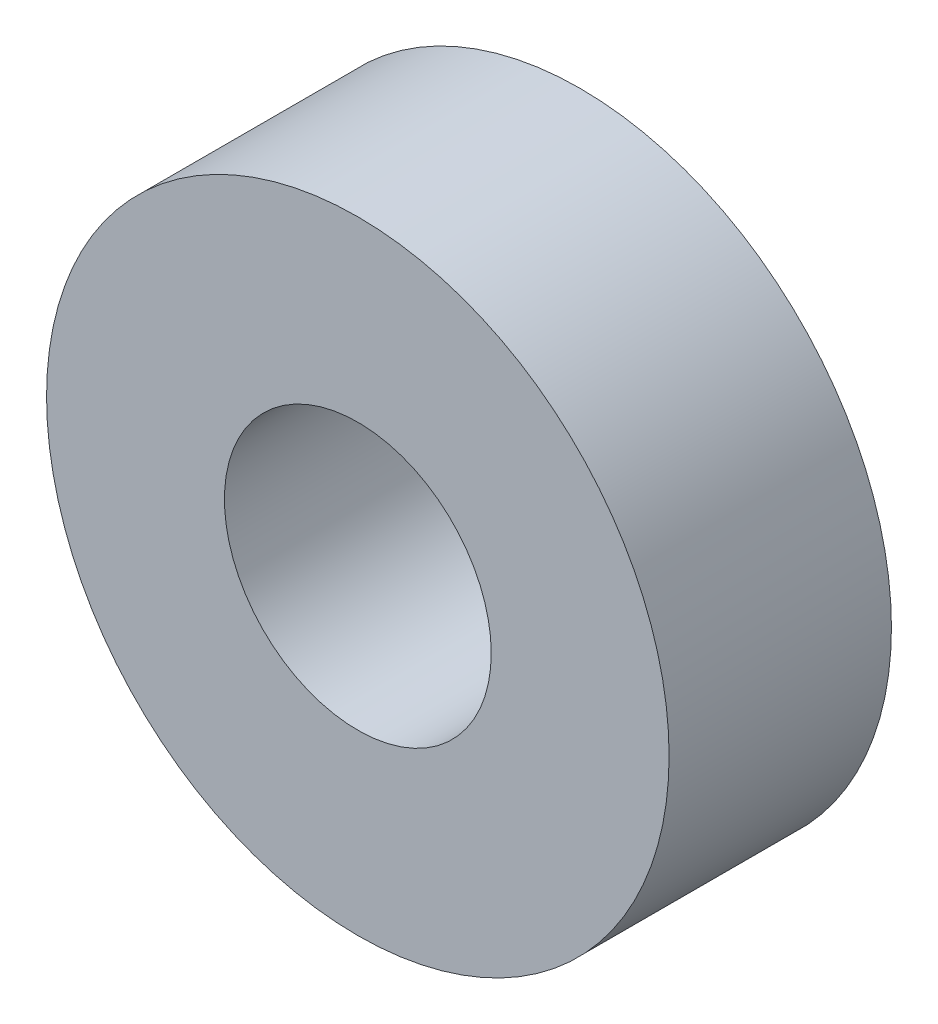
SolidWorks part; units mm, degrees
ref_plane "前视基准面" through (0, 0, 0) normal (0, 0, 1) x (1, 0, 0)
ref_plane "上视基准面" through (0, 0, 0) normal (0, 1, 0) x (1, 0, 0)
ref_plane "右视基准面" through (0, 0, 0) normal (1, 0, 0) x (0, 0, -1)
sketch "草图1" plane through (0, 0, 0) normal (0, 0, 1) x (1, 0, 0)
  circle A0 centre (0, 0) radius 7
  circle A1 centre (0, 0) radius 3
  dimension "D1" = 6
  dimension "D2" = 14
extrude "凸台-拉伸1" add sketch "草图1" along normal mid plane 5
